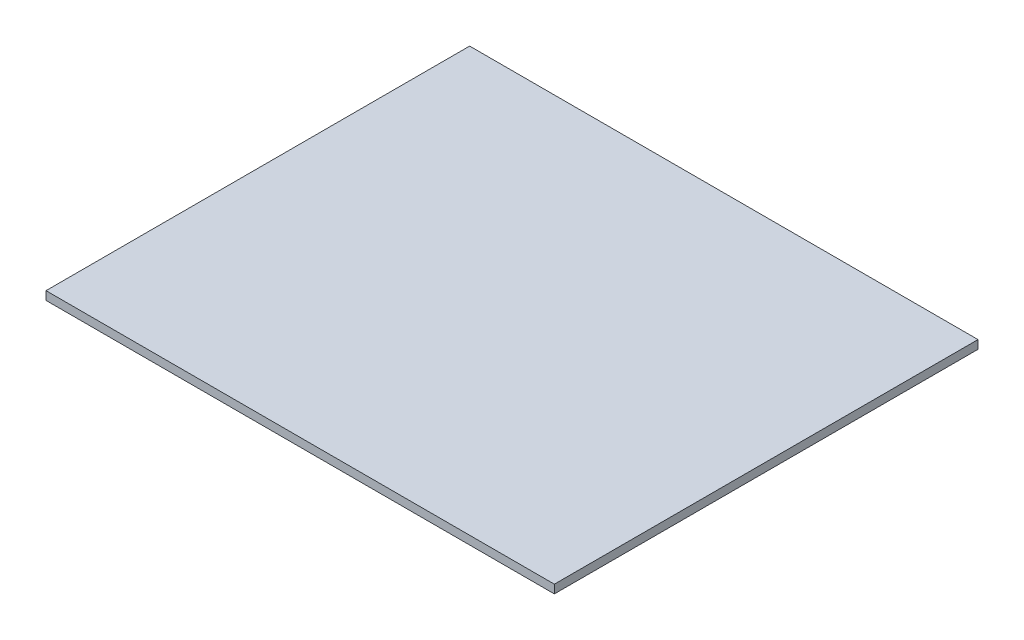
SolidWorks part; units mm, degrees
ref_plane "前视基准面" through (0, 0, 0) normal (0, 0, 1) x (1, 0, 0)
ref_plane "上视基准面" through (0, 0, 0) normal (0, 1, 0) x (1, 0, 0)
ref_plane "右视基准面" through (0, 0, 0) normal (1, 0, 0) x (0, 0, -1)
sketch "草图1" plane through (0, 0, 0) normal (0, 1, 0) x (1, 0, 0)
  line L0 (0, 0) -> (1200, 0)
  line L1 (1200, 0) -> (1200, -1000)
  line L2 (1200, -1000) -> (0, -1000)
  line L3 (0, -1000) -> (0, 0)
  dimension "D1" = 1200
  dimension "D2" = 1000
extrude "凸台-拉伸1" add sketch "草图1" along normal blind 20
